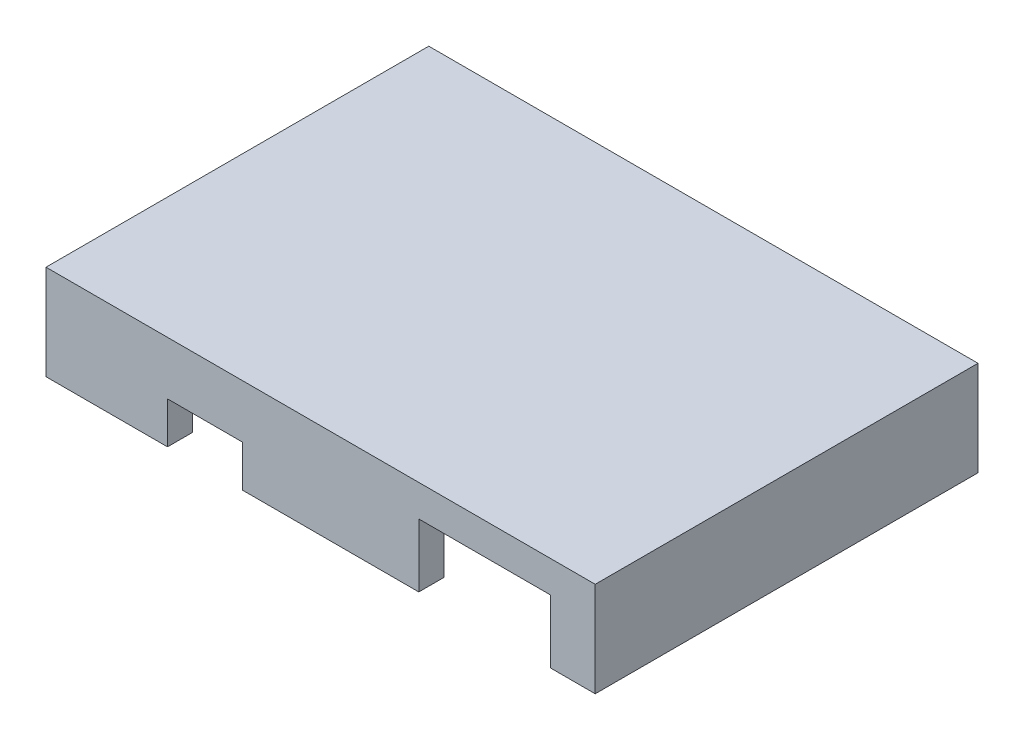
SolidWorks part; units mm, degrees
ref_plane "Front Plane" through (0, 0, 0) normal (0, 0, 1) x (1, 0, 0)
ref_plane "Top Plane" through (0, 0, 0) normal (0, 1, 0) x (1, 0, 0)
ref_plane "Right Plane" through (0, 0, 0) normal (1, 0, 0) x (0, 0, -1)
sketch "Sketch1" plane through (0, 0, 0) normal (0, 1, 0) x (1, 0, 0)
  line L0 (-16.5, -11.5) -> (-16.5, 11.5)
  line L1 (15, -10) -> (-15, -10)
  line L2 (15, -10) -> (15, 10)
  line L3 (15, 10) -> (-15, 10)
  line L4 (-15, -10) -> (-15, 10)
  line L5 (15, -10) -> (-15, 10) construction
  line L6 (15, 10) -> (-15, -10) construction
  line L7 (16.5, 11.5) -> (-16.5, 11.5)
  line L8 (16.5, -11.5) -> (16.5, 11.5)
  line L9 (16.5, -11.5) -> (-16.5, -11.5)
  point P0 (0, 0)
  dimension "D2" = 30
  dimension "D3" = 20
  dimension "D1" = 1.5
extrude "Boss-Extrude1" add sketch "Sketch1" along normal blind 5.7
sketch "Sketch2" plane through (0, 5.7, 0) normal (0, 1, 0) x (1, 0, 0)
  line L0 (15, -10) -> (15, 10) construction
  line L1 (-15, -10) -> (15, -10) construction
  line L2 (-15, 10) -> (-15, -10) construction
  line L3 (15, 10) -> (-15, 10) construction
  line L4 (15, -10) -> (15, 10)
  line L5 (-15, -10) -> (15, -10)
  line L6 (-15, 10) -> (-15, -10)
  line L7 (15, 10) -> (-15, 10)
extrude "Boss-Extrude2" add sketch "Sketch2" against normal blind 1.5
sketch "Sketch3" plane through (0, 0, -11.5) normal (0, 0, -1) x (-1, 0, 0)
  line L0 (-16.5, 0) -> (16.5, 0) construction
  line L1 (13.5, -1.8) -> (6, -1.8)
  line L2 (13.5, -1.8) -> (13.5, 1.8)
  line L3 (13.5, 1.8) -> (6, 1.8)
  line L4 (6, -1.8) -> (6, 1.8)
  line L5 (13.5, -1.8) -> (6, 1.8) construction
  line L6 (13.5, 1.8) -> (6, -1.8) construction
  line L7 (16.5, 5.7) -> (16.5, 0) construction
  point P0 (9.75, 0)
  dimension "D1" = 7.5
  dimension "D2" = 3
  dimension "D3" = 1.8
extrude "Cut-Extrude1" cut sketch "Sketch3" against normal up to next
sketch "Sketch4" plane through (0, 0, 11.5) normal (0, 0, 1) x (1, 0, 0)
  line L0 (-16.5, 0) -> (16.5, 0) construction
  line L1 (13.8, 3.8) -> (5.9, 3.8)
  line L2 (13.8, 3.8) -> (13.8, -3.8)
  line L3 (13.8, -3.8) -> (5.9, -3.8)
  line L4 (5.9, 3.8) -> (5.9, -3.8)
  line L5 (13.8, 3.8) -> (5.9, -3.8) construction
  line L6 (13.8, -3.8) -> (5.9, 3.8) construction
  line L7 (16.5, 5.7) -> (16.5, 0) construction
  line L8 (-16.5, 5.7) -> (-16.5, 0) construction
  line L9 (-4.7, 2.5) -> (-9.2, 2.5)
  line L10 (-4.7, 2.5) -> (-4.7, -2.5)
  line L11 (-4.7, -2.5) -> (-9.2, -2.5)
  line L12 (-9.2, 2.5) -> (-9.2, -2.5)
  line L13 (-4.7, 2.5) -> (-9.2, -2.5) construction
  line L14 (-4.7, -2.5) -> (-9.2, 2.5) construction
  point P0 (9.85, 0)
  point P9 (-6.95, 0)
  dimension "D1" = 3.8
  dimension "D2" = 2.7
  dimension "D3" = 7.9
  dimension "D4" = 7.3
  dimension "D5" = 11.8
  dimension "D6" = 2.5
extrude "Cut-Extrude2" cut sketch "Sketch4" against normal up to next
sketch "Sketch5" plane through (-16.5, 0, 0) normal (-1, 0, 0) x (0, 0, 1)
  line L0 (-11.5, 0) -> (11.5, 0) construction
  line L1 (3.5, 2.5) -> (6.85, 2.5)
  line L2 (3.5, 2.5) -> (3.5, -2.5)
  line L3 (3.5, -2.5) -> (6.85, -2.5)
  line L4 (6.85, 2.5) -> (6.85, -2.5)
  line L5 (3.5, 2.5) -> (6.85, -2.5) construction
  line L6 (3.5, -2.5) -> (6.85, 2.5) construction
  line L7 (11.5, 5.7) -> (11.5, 0) construction
  point P0 (5.175, 0)
  dimension "D1" = 2.5
  dimension "D2" = 4.65
  dimension "D3" = 8
extrude "Cut-Extrude3" cut sketch "Sketch5" against normal up to next
sketch "Sketch6" plane through (0, 4.2, 0) normal (0, -1, 0) x (1, 0, 0)
  line L1 (15, -10) -> (13, -10)
  line L2 (15, -10) -> (15, 2.5)
  line L3 (15, 2.5) -> (13, 2.5)
  line L4 (13, -10) -> (13, 2.5)
  dimension "D1" = 2
  dimension "D2" = 12.5
extrude "Boss-Extrude3" add sketch "Sketch6" along normal offset from surface (2.2 mm away) 2 up to face at (9.825, 0, 0)
sketch "Sketch7" plane through (0, 4.2, 0) normal (0, -1, 0) x (1, 0, 0)
  line L0 (-15, -10) -> (-15, 10) construction
  line L1 (-15, -6.6) -> (-13.8, -6.6)
  line L2 (-15, -6.6) -> (-15, -3.3)
  line L3 (-15, -3.3) -> (-13.8, -3.3)
  line L4 (-13.8, -6.6) -> (-13.8, -3.3)
  line L5 (-13.5, -10) -> (-6, -10) construction
  line L6 (-15, 10) -> (-13.8, 10)
  line L7 (-15, 10) -> (-15, 8.8)
  line L8 (-15, 8.8) -> (-13.8, 8.8)
  line L9 (-13.8, 10) -> (-13.8, 8.8)
  dimension "D1" = 1.2
  dimension "D2" = 3.4
  dimension "D3" = 6.7
extrude "Boss-Extrude4" add sketch "Sketch7" along normal offset from surface (3.2 mm away) 1 up to face at (-15, 0, -6)
